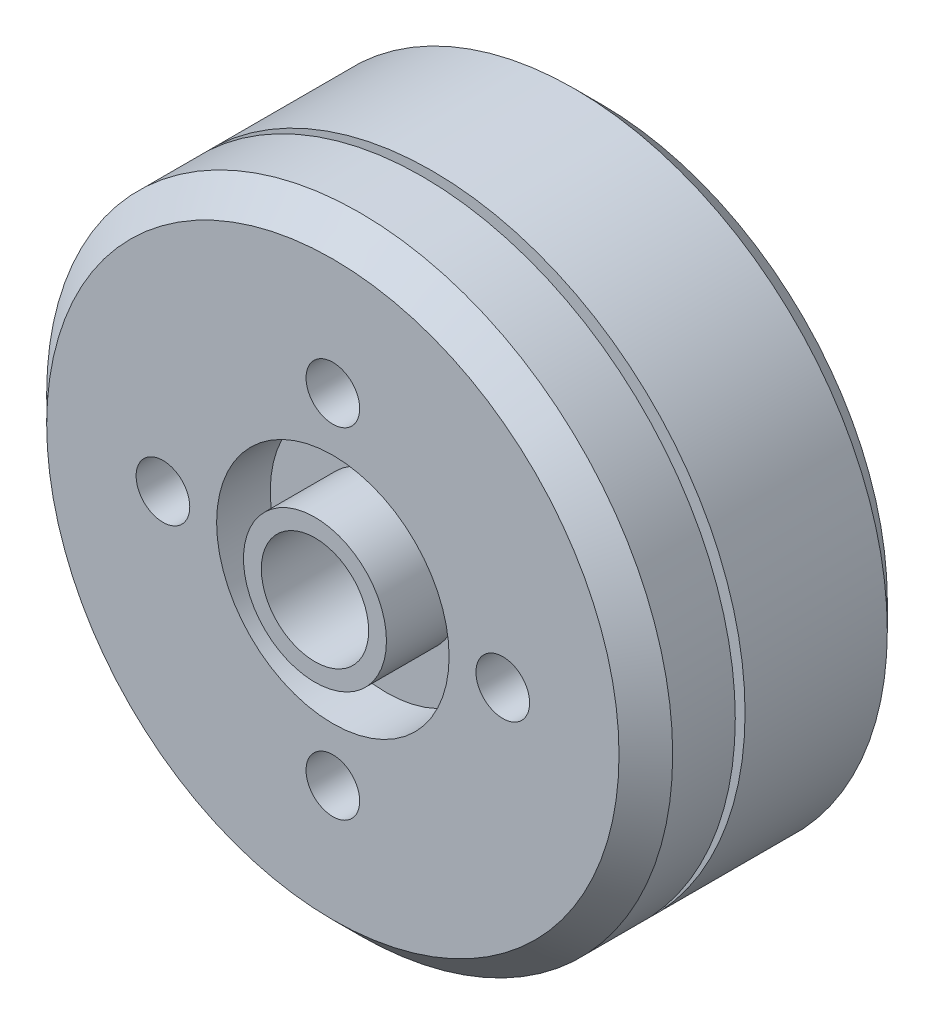
SolidWorks part; units mm, degrees
ref_plane "前视基准面" through (0, 0, 0) normal (0, 0, 1) x (1, 0, 0)
ref_plane "上视基准面" through (0, 0, 0) normal (0, 1, 0) x (1, 0, 0)
ref_plane "右视基准面" through (0, 0, 0) normal (1, 0, 0) x (0, 0, -1)
sketch "草图1" plane through (0, 0, 0) normal (0, 0, 1) x (1, 0, 0)
  circle A0 centre (0, 0) radius 17.5
extrude "凸台-拉伸1" add sketch "草图1" along normal blind 15
sketch "草图2" plane through (0, 0, 0) normal (0, 0, -1) x (-1, 0, 0)
  circle A0 centre (0, -8) radius 1.5
  circle A1 centre (-8, 0) radius 1.5
  circle A2 centre (0, 8) radius 1.5
  circle A3 centre (8, 0) radius 1.5
  point P12 (0, 0)
  dimension "D1" = 4
extrude "切除-拉伸1" cut sketch "草图2" against normal blind 5
sketch "草图3" plane through (0, 0, 0) normal (0, 1, 0) x (1, 0, 0)
  line L2 (-17.5, -7.5) -> (17.5, -7.5) construction
  line L12 (0, 0) -> (0, -15)
  line L13 (-17.5, -15) -> (17.5, -15) construction
  line L14 (-17.5, 0) -> (-17.5, -15) construction
  line L15 (17.5, -15) -> (17.5, 0) construction
  line L16 (13.2844, -10) -> (13.2844, -9.9531)
  line L17 (13.2844, -9.4531) -> (17.9693, -9.4531)
  line L18 (13.2844, -9.9531) -> (13.2844, -9.4531)
  line L19 (17.9693, -10) -> (13.2844, -10)
  line L20 (17.9693, -10) -> (17.9693, -9.4531)
revolve "切除-旋转1" cut sketch "草图3" angle 360 about L12
sketch "草图4" plane through (0, 0, 0) normal (0, 0, -1) x (-1, 0, 0)
  circle A0 centre (0, 0) radius 3
extrude "切除-拉伸2" cut sketch "草图4" against normal blind 20
sketch "草图5" plane through (0, 0, 15) normal (0, 0, 1) x (1, 0, 0)
  circle A0 centre (0, -9.5) radius 1.5
  circle A1 centre (-9.5, 0) radius 1.5
  circle A2 centre (0, 9.5) radius 1.5
  circle A3 centre (9.5, 0) radius 1.5
  point P12 (0, 0)
  dimension "D1" = 4
extrude "切除-拉伸3" cut sketch "草图5" against normal blind 6
chamfer "倒角1" distance 1.5 angle 45 2 edges at (17.5, 0, 15) (17.5, 0, 0)
sketch "草图6" plane through (0, 0, 15) normal (0, 0, 1) x (1, 0, 0)
  circle A0 centre (0, 0) radius 6.5
  circle A1 centre (0, 0) radius 3.9966
extrude "切除-拉伸4" cut sketch "草图6" against normal blind 3
sketch "草图7" plane through (0, 0, 15) normal (0, 0, 1) x (1, 0, 0)
  circle A0 centre (0, 0) radius 3
  circle A1 centre (0, 0) radius 3.9966
extrude "凸台-拉伸2" add sketch "草图7" along normal blind 1
